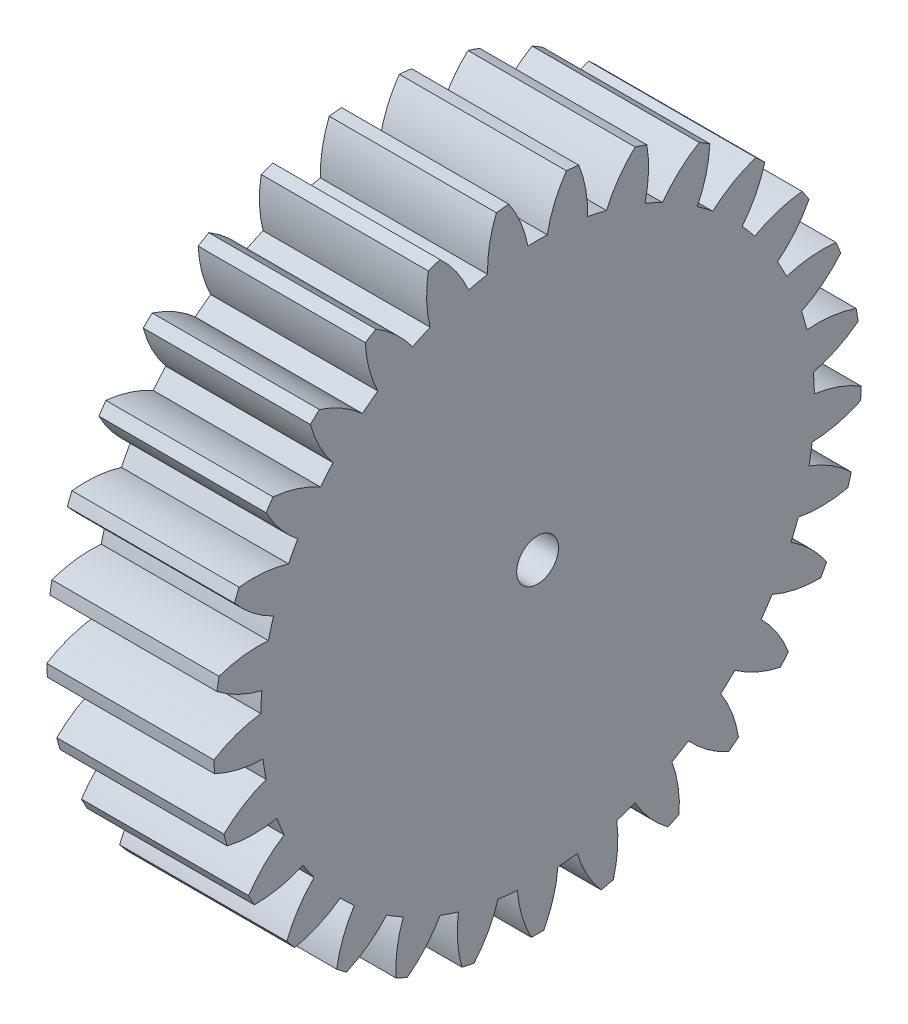
SolidWorks part; units mm, degrees
ref_plane "Plane1" through (0, 0, 0) normal (0, 0, 1) x (1, 0, 0)
ref_plane "Plane2" through (0, 0, 0) normal (0, 1, 0) x (1, 0, 0)
ref_plane "Plane3" through (0, 0, 0) normal (1, 0, 0) x (0, 0, -1)
sketch "HoldingSke" plane through (0, 0, 0) normal (0, 1, 0) x (1, 0, 0)
  line L0 (0, 0) -> (0.3498, -0.1939)
  line L1 (-15, 0) -> (100, 0) construction
  line L2 (0, 0) -> (-2.1039, 2.3779)
  line L3 (0, 0) -> (-11.863, 4.5341)
  line L4 (0, 0) -> (7.5532, 4.1868)
  line L5 (0, 0) -> (-46.8476, -17.4728)
  line L6 (0, 0) -> (-16.5793, -11.1861)
  line L7 (-2.1039, 2.3779) -> (8.6586, 51.2059)
  line L8 (-76.2, 54.61) -> (-75.3, 54.61)
  line L9 (-71.009, 38.7566) -> (-53.1078, 45.2721)
  line L10 (-76.2, 71.12) -> (104.1128, 71.12)
  line L11 (0, 0) -> (-20, 0)
  line L12 (-76.2, 101.6) -> (-76.113, 101.6)
  line L13 (24.9733, 27.94) -> (52.9518, 28.4284)
  line L14 (24.9733, 27.94) -> (24.9743, 27.94)
  line L15 (24.9733, 27.94) -> (100.4006, 29.5858)
  line L16 (-63.627, -2.5) -> (-12.827, -2.5)
  circle A0 centre (0, 0) radius 2.5
  circle A1 centre (0, 0) radius 33.124
  circle A2 centre (0, 0) radius 37.5
  circle A3 centre (0, 0) radius 2.5
  dimension "MHD" = 66.248
  dimension "Hub_dia" = 75
  dimension "Bore" = 5
  dimension "MBD" = 5
  dimension "Num_teeth" = 29
  dimension "Pitch" = 0.4
  dimension "Overall_len" = 50
  dimension "Show_teeth" = 29
  dimension "Thickness" = 20
  dimension "OAL" = 50.0001
  dimension "T_dim" = 0.9
  dimension "Ap" = 20
  dimension "H" = 19.05
  dimension "Pitch_radius" = 180.3128
  dimension "Width" = 20
  dimension "Backlash" = 0.087
  dimension "Addendum_fac" = 1
  dimension "Dedendum_fac" = 1.25
  dimension "Clearance_fac" = 0.25
  dimension "Dedendum_add" = 0.001
  dimension "Module" = 2.5
sketch "BasProSke" plane through (0, 0, 0) normal (0, 1, 0) x (1, 0, 0)
  line L0 (-10, 0) -> (60, 0) construction
  line L1 (0, 0) -> (0, 38.75)
  line L2 (0, 0) -> (20, 0)
  line L3 (20, 0) -> (20, 38.75)
  line L4 (20, 38.75) -> (0, 38.75)
  dimension "Thickness" = 20
  dimension "Diameter" = 77.5
revolve "Base-Revolve" add sketch "BasProSke" angle 360 about L0
sketch "TooCutSke" plane through (0, 0, 0) normal (1, 0, 0) x (0, 0, -1)
  line L1 (0, 0) -> (0, 107) construction
  line L2 (0, 0) -> (-2.1148, 36.1883) construction
  line L3 (0, 0) -> (-7.8288, 71.9851) construction
  line L4 (-2.1148, 36.1883) -> (-3.9144, 35.9925) construction
  arc A0 (1.1595, 33.1037) -> (-1.1595, 33.1037) centre (0, 0) ccw
  arc A1 (3.4687, 38.6199) -> (-3.4687, 38.6199) centre (0, 0) ccw
  circle A2 centre (0, 0) radius 36.25 construction
  circle A3 centre (0, 0) radius 34.0639 construction
  arc A4 (-1.1595, 33.1037) -> (-3.4687, 38.6199) centre (-15.4019, 30.383) ccw
  arc A5 (3.4687, 38.6199) -> (1.1595, 33.1037) centre (15.4019, 30.383) ccw
  dimension "Root_dia" = 66.248
  dimension "Overcut_dia" = 77.5508
  dimension "Pitch_dia" = 72.5
  dimension "Base_dia" = 68.1277
  dimension "Flank_rad" = 14.5
  dimension "Half_ang" = 6.207
  dimension "Half_CT" = 1.8103
extrude "ToothCut" cut sketch "TooCutSke" along normal through all
fillet "Breaks" [suppressed] radius 0.05
fillet "RootFillets" [suppressed] radius 0.626
pattern_circular "TeethCuts" count 29 every 12.414 about axis through (-10, 0, 0) along (1, 0, 0) of "ToothCut", "RootFillets", "Breaks"
sketch "HubNeaOneSke" plane through (0, 0, 0) normal (-1, 0, 0) x (0, 0, 1)
  circle A0 centre (0, 0) radius 33.124
  dimension "Diameter" = 66.248
extrude "HubNearOne" [suppressed] add sketch "HubNeaOneSke" along normal blind 30.0001
sketch "HubNeaBotSke" plane through (0, 0, 0) normal (-1, 0, 0) x (0, 0, 1)
  circle A0 centre (0, 0) radius 33.124
  dimension "Diameter" = 66.248
extrude "HubNearBoth" [suppressed] add sketch "HubNeaBotSke" along normal blind 15
ref_plane "FarPln" through (20, 0, 0) normal (1, 0, 0) x (0, 0, -1)
sketch "HubFarSke" plane through (20, 0, 0) normal (1, 0, 0) x (0, 0, -1)
  circle A0 centre (0, 0) radius 33.124
  dimension "Diameter" = 66.248
extrude "HubFar" [suppressed] add sketch "HubFarSke" along normal blind 15
sketch "BorSke" plane through (0, 0, 0) normal (1, 0, 0) x (0, 0, -1)
  circle A0 centre (0, 0) radius 2.5
  dimension "Diameter" = 5
extrude "Bore" cut sketch "BorSke" along normal mid plane 100.0001
sketch "KeySke" plane through (0, 0, 0) normal (1, 0, 0) x (0, 0, -1)
  line L0 (-1, 0) -> (-1, 3.4)
  line L1 (-1, 3.4) -> (1, 3.4)
  line L2 (1, 3.4) -> (1, 0)
  line L3 (0, 0) -> (0, 34) construction
  line L4 (-1, 0) -> (1, 0)
  dimension "Offset" = 3.4
extrude "Keyway" [suppressed] cut sketch "KeySke" along normal mid plane 100.0001
pattern_circular "Keyway2" [suppressed] count 2 every 90 about axis through (-10, 0, 0) along (1, 0, 0)
equation "' \"Module@HoldingSke\" = 6.35"
equation "' \"Num_teeth@HoldingSke\" = 12"
equation "' \"Ap@HoldingSke\" =  20"
equation "' \"Ap@HoldingSke\" = 20"
equation "' \"Width@HoldingSke\" = 0.5 * 25.4"
equation "' \"Hub_dia@HoldingSke\"= 1 * 25.4"
equation "' \"Hub_dia@HoldingSke\" = 1 * 25.4"
equation "' \"Overall_len@HoldingSke\" = 1.0 * 25.4"
equation "' \"Bore@HoldingSke\" = 0.75 * 25.4"
equation "' \"T_dim@HoldingSke\" = 0.1 * 25.4"
equation "' \"Width@KeySke\" = 0.25 * 25.4"
equation "' \"Show_teeth@HoldingSke\" = 13"
equation "' \"Backlash@HoldingSke\" = 0.009 * 25.4"
equation "' \"Addendum_fac@HoldingSke\" = 1.0"
equation "' \"Dedendum_fac@HoldingSke\" = 1.25"
equation "' \"Dedendum_add@HoldingSke\" = 0.00005 * 25.4"
equation "' \"Clearance_fac@HoldingSke\" = 0.25"
equation "\"Pitch@HoldingSke\" = 1 / \"Module@HoldingSke\""
equation "\"Overcut_dia@TooCutSke\" = (\"Num_teeth@HoldingSke\" + 2 * \"Addendum_fac@HoldingSke\") / \"Pitch@HoldingSke\" + 0.002 * 25.4"
equation "\"Pitch_dia@TooCutSke\" = \"Num_teeth@HoldingSke\" / \"Pitch@HoldingSke\""
equation "\"Base_dia@TooCutSke\" = \"Num_teeth@HoldingSke\" / \"Pitch@HoldingSke\" * cos((\"Ap@HoldingSke\"  * 3.14159265 / 180))"
equation "\"Root_dia@TooCutSke\" = (\"Num_teeth@HoldingSke\" + 2) / \"Pitch@HoldingSke\" - 2 * (\"Addendum_fac@HoldingSke\" + \"Dedendum_fac@HoldingSke\") / \"Pitch@HoldingSke\" - \"Dedendum_add@HoldingSke\" * 2"
equation "\"Half_ang@TooCutSke\" = 180 / \"Num_teeth@HoldingSke\""
equation "\"Half_CT@TooCutSke\" = \"Num_teeth@HoldingSke\" / \"Pitch@HoldingSke\" * sin((3.14159265 / 2 / \"Num_teeth@HoldingSke\")) / 2 - 7 * \"Backlash@HoldingSke\" / 4"
equation "\"Flank_rad@TooCutSke\" = \"Num_teeth@HoldingSke\" / \"Pitch@HoldingSke\" / 5"
equation "\"Radius@RootFillets\" = \"Clearance_fac@HoldingSke\" / \"Pitch@HoldingSke\" + \"Dedendum_add@HoldingSke\""
equation "\"Break_rad@Breaks\" = 0.02 / \"Pitch@HoldingSke\""
equation "\"Thickness@HoldingSke\" = \"Width@HoldingSke\""
equation "\"OAL@HoldingSke\" = \"Thickness@HoldingSke\""
equation "\"MHD@HoldingSke\" = (\"Num_teeth@HoldingSke\" + 2) / \"Pitch@HoldingSke\" - 2 * (\"Addendum_fac@HoldingSke\" + \"Dedendum_fac@HoldingSke\")  / \"Pitch@HoldingSke\" - \"Dedendum_add@HoldingSke\" * 2"
equation "\"MBD@HoldingSke\" = (\"Num_teeth@HoldingSke\" + 2) / \"Pitch@HoldingSke\" - 2 * (\"Addendum_fac@HoldingSke\" + \"Dedendum_fac@HoldingSke\")  / \"Pitch@HoldingSke\" - \"Dedendum_add@HoldingSke\" * 2 - 0.002 * 25.4"
equation "\"MHD@HoldingSke\" = ((sgn( \"MHD@HoldingSke\" - \"Hub_dia@HoldingSke\" )-1)*( \"MHD@HoldingSke\" - \"Hub_dia@HoldingSke\" ))/-2+ \"Hub_dia@HoldingSke\""
equation "\"MBD@HoldingSke\" = ((sgn( \"MBD@HoldingSke\" - \"Bore@HoldingSke\" )-1)*( \"MBD@HoldingSke\" - \"Bore@HoldingSke\" ))/-2+ \"Bore@HoldingSke\""
equation "\"OAL@HoldingSke\" = ((sgn( \"OAL@HoldingSke\" - \"Overall_len@HoldingSke\" )+1)*( \"OAL@HoldingSke\" - \"Overall_len@HoldingSke\" ))/2 + \"Overall_len@HoldingSke\" + 0.000002 * 25.4"
equation "\"Num_teeth@TeethCuts\" = int( \"Show_teeth@HoldingSke\" ) + 1"
equation "\"Num_teeth@TeethCuts\" = ((sgn( \"Num_teeth@TeethCuts\" - \"Num_teeth@HoldingSke\" )-1)*( \"Num_teeth@TeethCuts\" - \"Num_teeth@HoldingSke\" ))/-2+ \"Num_teeth@HoldingSke\""
equation "\"Num_teeth@TeethCuts\" = ((sgn( \"Num_teeth@TeethCuts\" - 2.0)+1)*( \"Num_teeth@TeethCuts\" - 2.0))/2 +2.0"
equation "\"Angle@TeethCuts\" = 360.0 / \"Num_teeth@HoldingSke\""
equation "\"Diameter@BasProSke\" = (\"Num_teeth@HoldingSke\" + 2 * \"Addendum_fac@HoldingSke\") / \"Pitch@HoldingSke\""
equation "\"Thickness@BasProSke\"  = \"Thickness@HoldingSke\""
equation "' \"Fillet_rad@BasProSke\" =  \"Thickness@HoldingSke\" * 0.05"
equation "' \"Fillet_rad@BasProSke\" = \"Thickness@HoldingSke\" * 0.05"
equation "\"MHD@HoldingSke\" = ((sgn( \"MHD@HoldingSke\" - \"Root_dia@TooCutSke\" )-1)*( \"MHD@HoldingSke\" - \"Root_dia@TooCutSke\" ))/-2+ \"Root_dia@TooCutSke\""
equation "\"Diameter@HubNeaOneSke\" = \"MHD@HoldingSke\""
equation "\"Length@HubNearOne\" = \"OAL@HoldingSke\" - \"Thickness@BasProSke\""
equation "\"Diameter@HubNeaBotSke\" = \"MHD@HoldingSke\""
equation "\"Length@HubNearBoth\" = ( \"OAL@HoldingSke\" - \"Thickness@BasProSke\" ) / 2.0"
equation "\"Thickness@FarPln\" = \"Thickness@BasProSke\""
equation "\"Diameter@HubFarSke\" = \"MHD@HoldingSke\""
equation "\"Length@HubFar\" = ( \"OAL@HoldingSke\" - \"Thickness@BasProSke\" ) / 2.0"
equation "\"Diameter@BorSke\" = \"MBD@HoldingSke\""
equation "\"D1@Bore\" = \"OAL@HoldingSke\" * 2.0"
equation "\"D1@Keyway\" = \"OAL@HoldingSke\" * 2.0"
equation "\"Offset@KeySke\" = \"T_dim@HoldingSke\" + \"MBD@HoldingSke\" / 2.0"
